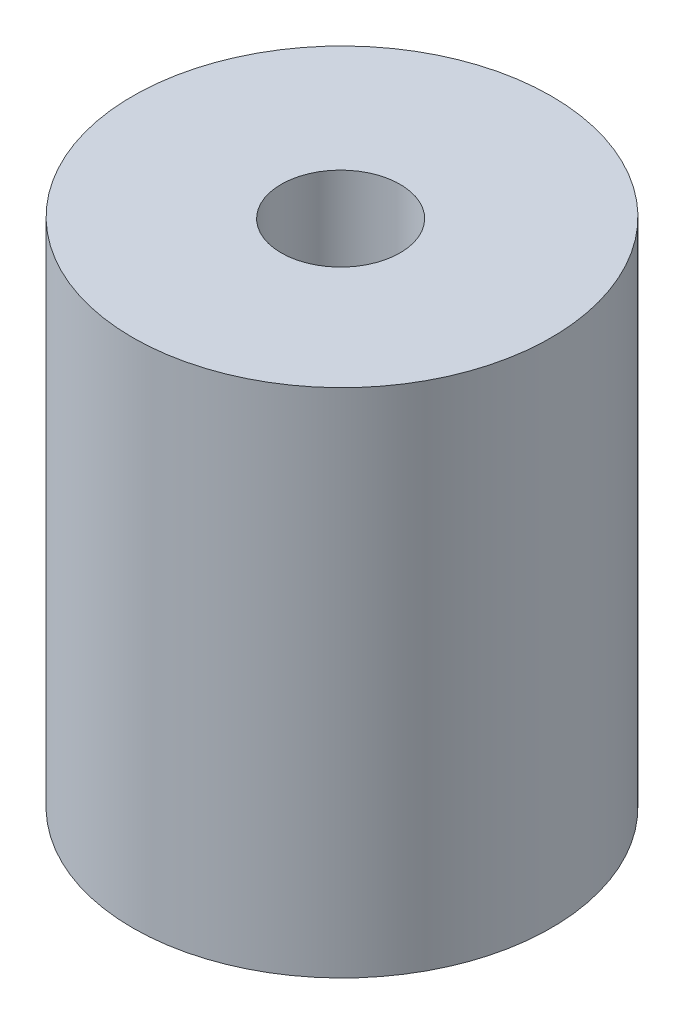
SolidWorks part; units mm, degrees
material "Alloy Steel"
ref_plane "Front Plane" through (0, 0, 0) normal (0, 0, 1) x (1, 0, 0)
ref_plane "Top Plane" through (0, 0, 0) normal (0, 1, 0) x (1, 0, 0)
ref_plane "Right Plane" through (0, 0, 0) normal (1, 0, 0) x (0, 0, -1)
sketch "Sketch1" plane through (0, 0, 0) normal (0, 1, 0) x (1, 0, 0)
  circle A0 centre (-10.5852, 13.3708) radius 22.352
  circle A1 centre (-10.5852, 13.3708) radius 6.35
extrude "Boss-Extrude1" add sketch "Sketch1" along normal blind 54.61 contours A0
sketch "Sketch2" plane through (0, 54.61, 0) normal (0, 1, 0) x (1, 0, 0)
  circle A0 centre (-10.4935, 13.1334) radius 6.35
extrude "Cut-Extrude1" cut sketch "Sketch2" against normal blind 20.6502
sketch "Sketch3" plane through (0, 0, 0) normal (0, -1, 0) x (-1, 0, 0)
  circle A0 centre (10.4935, 13.1334) radius 6.35
extrude "Cut-Extrude2" cut sketch "Sketch3" against normal blind 20.6502
